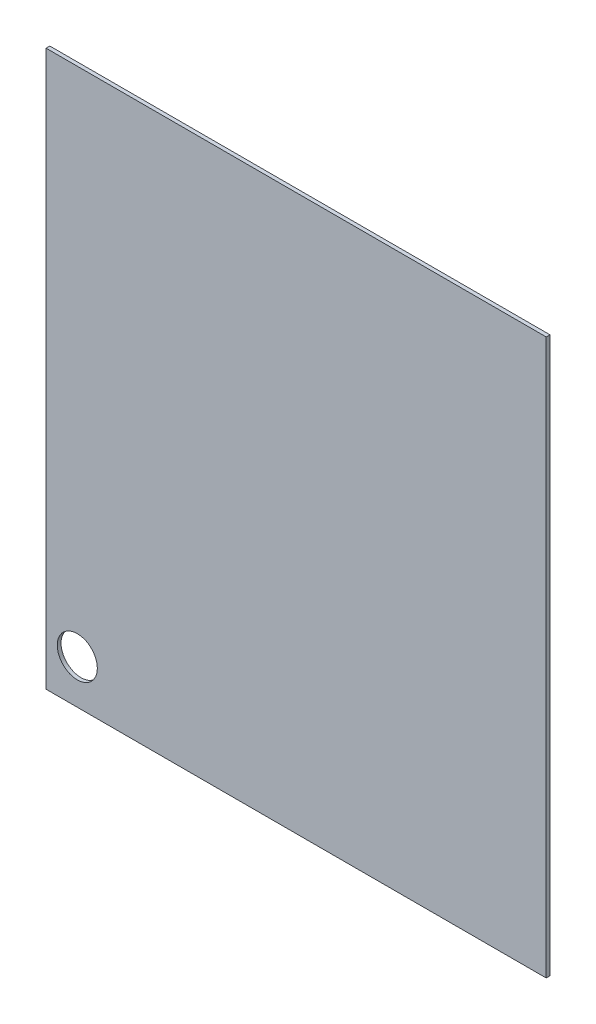
SolidWorks part; units mm, degrees
ref_plane "Front Plane" through (0, 0, 0) normal (0, 0, 1) x (1, 0, 0)
ref_plane "Top Plane" through (0, 0, 0) normal (0, 1, 0) x (1, 0, 0)
ref_plane "Right Plane" through (0, 0, 0) normal (1, 0, 0) x (0, 0, -1)
sketch "Sketch1" plane through (0, 0, 0) normal (0, 0, 1) x (1, 0, 0)
  line L1 (0, 0) -> (400, 0)
  line L2 (0, 0) -> (0, 452)
  line L3 (0, 452) -> (400, 452)
  line L4 (400, 0) -> (400, 452)
  dimension "D1" = 400
  dimension "D2" = 452
extrude "Boss-Extrude1" add sketch "Sketch1" along normal blind 3
sketch "Sketch4" plane through (0, 0, 3) normal (0, 0, 1) x (1, 0, 0)
  line L0 (0, 0) -> (400, 0) construction
  line L1 (0, 452) -> (0, 0) construction
  circle A0 centre (25, 35) radius 16
  dimension "D1" = 32
  dimension "D2" = 35
  dimension "D3" = 25
extrude "Cut-Extrude2" cut sketch "Sketch4" against normal blind 10
sketch "Sketch5" plane through (0, 0, 0) normal (0, 0, -1) x (-1, 0, 0)
  line L0 (-400, 452) -> (0, 452) construction
  line L1 (0, 452) -> (-400, 452)
  line L2 (0, 452) -> (0, 444)
  line L3 (0, 444) -> (-400, 444)
  line L4 (-400, 452) -> (-400, 444)
  line L5 (-400, 0) -> (-400, 452) construction
  line L6 (0, 452) -> (0, 0) construction
  dimension "D1" = 8
extrude "Cut-Extrude3" cut sketch "Sketch5" against normal through all
